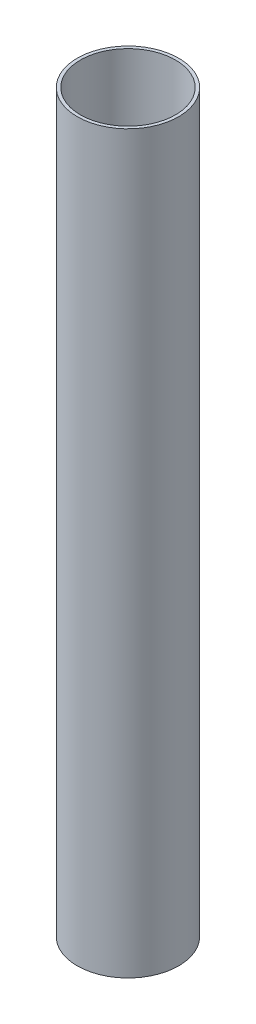
SolidWorks part; units mm, degrees
ref_plane "前视基准面" through (0, 0, 0) normal (0, 0, 1) x (1, 0, 0)
ref_plane "上视基准面" through (0, 0, 0) normal (0, 1, 0) x (1, 0, 0)
ref_plane "右视基准面" through (0, 0, 0) normal (1, 0, 0) x (0, 0, -1)
sketch "草图1" plane through (0, 0, 0) normal (0, 1, 0) x (1, 0, 0)
  circle A0 centre (0, 0) radius 16
  circle A1 centre (0, 0) radius 15
extrude "凸台-拉伸1" add sketch "草图1" along normal blind 232 contours A0 | A1
